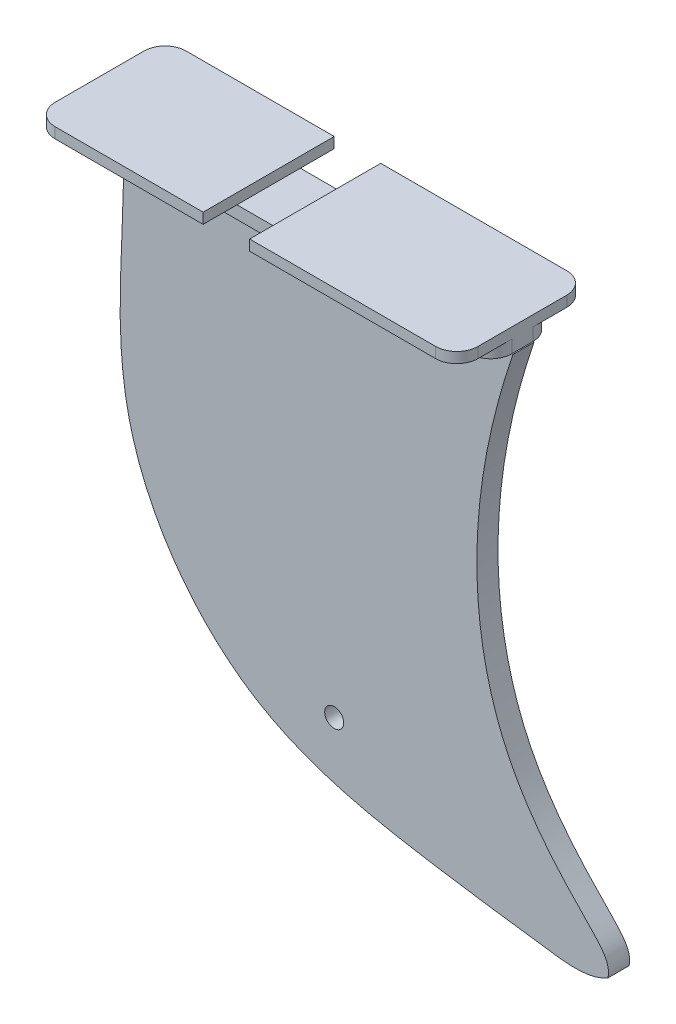
SolidWorks part; units mm, degrees
ref_plane "Alzado" through (0, 0, 0) normal (0, 0, 1) x (1, 0, 0)
ref_plane "Planta" through (0, 0, 0) normal (0, 1, 0) x (1, 0, 0)
ref_plane "Vista lateral" through (0, 0, 0) normal (1, 0, 0) x (0, 0, -1)
sketch "Croquis1" plane through (0, 0, 0) normal (0, 1, 0) x (1, 0, 0)
  line L1 (-50, -15.5) -> (50, -15.5)
  line L2 (-50, -15.5) -> (-50, 15.5)
  line L3 (-50, 15.5) -> (50, 15.5)
  line L4 (50, -15.5) -> (50, 15.5)
  line L5 (-50, -15.5) -> (50, 15.5) construction
  line L6 (-50, 15.5) -> (50, -15.5) construction
  point P0 (0, 0)
  dimension "D1" = 31
  dimension "D2" = 100
extrude "Saliente-Extruir1" add sketch "Croquis1" along normal blind 2.5
sketch "Croquis2" plane through (0, 0, 0) normal (0, -1, 0) x (1, 0, 0)
  line L0 (50, 15.5) -> (50, -15.5) construction
  line L1 (50, 7.5) -> (-42, 7.5)
  line L2 (50, 7.5) -> (50, -7.5)
  line L3 (50, -7.5) -> (-42, -7.5)
  line L4 (-42, 7.5) -> (-42, -7.5)
  line L7 (-50, -15.5) -> (-50, 15.5) construction
  point P6 (-42, 0)
  dimension "D1" = 15
  dimension "D2" = 8
extrude "Saliente-Extruir2" add sketch "Croquis2" along normal blind 3
fillet "Redondeo1" radius 5 8 edges at (50, 1.25, 15.5) (50, -1.5, 7.5) (50, -1.5, -7.5) (50, 1.25, -15.5) (-50, 1.25, -15.5) (-42, -1.5, -7.5) (-42, -1.5, 7.5) (-50, 1.25, 15.5)
sketch "Croquis3" plane through (0, 0, 0) normal (0, 0, 1) x (1, 0, 0)
  line L0 (50.2687, -3) -> (-42, -3)
  line L1 (45, -3) -> (50, -3) construction
  spline S0 degree 3 poles (-42, -3) (-40.9085, -23.2943) (-48.7763, -61.4392) (-15.0116, -108.4968) (26.0913, -116.272) (53.9217, -120.1729) (68.331, -122.0767) (72.7453, -119.458) knots 0 0 0 0 0.313172 0.560687 0.787562 0.924725 1 1 1 1
  spline S1 degree 3 poles (72.7453, -119.458) (73.5273, -115.2951) (67.8664, -111.5642) (40.8374, -79.6561) (38.3699, -37.7895) (50.2687, -3) knots 0 0 0 0 0.326989 0.554852 1 1 1 1
  point P7 (64.2438, -99.4521)
  point P10 (36.8225, -44.4001)
  point P13 (42.2649, -74.9613)
  point P15 (-13.8337, -116.8259)
  point P16 (21.7513, -135.8743)
  point P18 (64.6625, -142.9913)
  point P19 (91.058, -138.0624)
  point P20 (99.1585, -130.3066)
  point P21 (0, 0)
  point P22 (76.4081, -112.8991)
  point P23 (52.279, -79.9801)
  point P25 (-6.6766, -118.2929)
  point P26 (36.8268, -136.9093)
  point P27 (71.708, -142.3962)
  point P28 (52.5038, -91.0542)
  point P29 (44.8613, -68.1267)
  point P30 (56.0311, -100.2644)
  point P31 (69.7484, -141.0245)
  point P32 (39.1784, -132.0102)
  point P33 (65.6332, -133.7739)
  point P34 (76.4081, -132.4021)
  point P35 (81.3101, -126.9152)
  point P36 (73.0797, -118.2929)
  point P37 (-37, -3)
  point P38 (-42, -3)
  point P40 (45, -3)
  point P41 (50, -3)
  point P44 (-39.7437, -64.4575)
  point P45 (0, 0)
  point P46 (-8.3634, -108.1437)
  point P47 (33.8871, -119.8344)
  point P48 (60.7552, -124.9619)
  point P49 (70.3949, -123.7313)
  point P50 (48.2441, -84.9674)
  point P51 (41.4758, -51.7413)
  point P52 (72.8561, -122.9109)
  point P53 (0, 0)
  point P54 (63.3439, -106.7604)
  point P55 (0, 0)
  point P56 (60.3416, -122.6094)
  point P57 (70.9058, -122.1462)
  point P58 (0, 0)
  point P59 (72.951, -120.2388)
  point P60 (-10.9837, -103.6555)
  point P61 (31.5751, -116.8704)
  point P62 (58.2389, -120.7297)
  point P63 (69.115, -120.9051)
  point P64 (72.7453, -119.458)
extrude "Saliente-Extruir3" add sketch "Croquis3" along normal mid plane 5
sketch "Croquis4" plane through (0, 0, 2.5) normal (0, 0, 1) x (1, 0, 0)
  line L0 (8, -8.5) -> (8, -98.5) construction
  line L1 (8, -6.25) -> (8, -3) construction
  line L2 (45, -3) -> (-37, -3) construction
  line L3 (8, -8.5) -> (8, -3) construction
  circle A0 centre (8, -8.5) radius 2.25
  circle A1 centre (8, -98.5) radius 2.25
  dimension "D3" = 4.5
  dimension "D1" = 90
  dimension "D2" = 8
  dimension "D4" = 5.5
extrude "Cortar-Extruir1" cut sketch "Croquis4" against normal blind 5
sketch "Croquis5" plane through (0, 0, 15.5) normal (0, 0, 1) x (1, 0, 0)
  line L0 (-45, 2.5) -> (45, 2.5) construction
  line L1 (-10, 2.5) -> (1, 2.5)
  line L2 (-10, 2.5) -> (-10, 0)
  line L3 (-10, 0) -> (1, 0)
  line L4 (1, 2.5) -> (1, 0)
  line L5 (45, 0) -> (-37, 0) construction
  line L6 (-42, -3) -> (-42, 0) construction
  dimension "D1" = 32
  dimension "D2" = 11
extrude "Cortar-Extruir2" cut sketch "Croquis5" against normal through all
